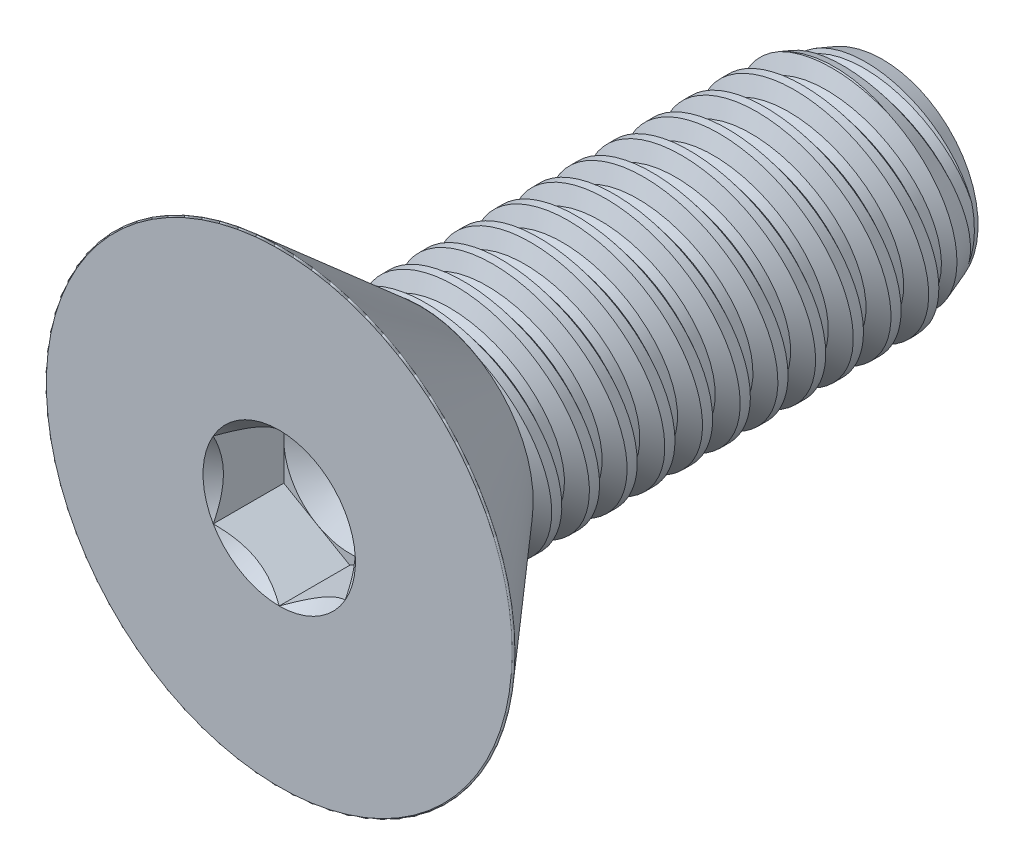
SolidWorks part; units mm, degrees
material "Plain Carbon Steel"
ref_plane "Front" through (0, 0, 0) normal (0, 0, 1) x (1, 0, 0)
ref_plane "Top" through (0, 0, 0) normal (0, 1, 0) x (1, 0, 0)
ref_plane "Right" through (0, 0, 0) normal (1, 0, 0) x (0, 0, -1)
sketch "Sketch1" plane through (0, 0, 0) normal (1, 0, 0) x (0, 0, -1)
  line L0 (0, 0) -> (-5.9436, 0) construction
  line L1 (0, 0) -> (19.4564, 0)
  line L2 (0, 0) -> (0, 4.7625)
  line L3 (0, 4.7625) -> (19.4564, 4.7625)
  line L4 (19.4564, 0) -> (19.4564, 4.7625)
  line L5 (0, -4.7625) -> (19.4564, -4.7625) construction
  dimension "D1" = 19.4564
  dimension "Thread Dia" = 9.525
  dimension "Length" = 25.4
  dimension "Head Height" = 5.9436
revolve "Revolve1" add sketch "Sketch1" angle 360 about L0
ref_plane "Plane1" through (0, 0, 5.9436) normal (0, 0, 1) x (1, 0, 0)
sketch "Sketch2" plane through (0, 0, 0) normal (1, 0, 0) x (0, 0, -1)
  line L0 (0, 4.7625) -> (0, -4.7625) construction
  line L1 (0, -4.7625) -> (1.5875, -4.7625) construction
  line L2 (1.5875, -4.7625) -> (0, 4.7625) construction
  line L3 (0, 4.7625) -> (0.1957, 4.7951) construction
  line L4 (0.1957, 4.7951) -> (1.5659, 5.0235)
  line L5 (1.5659, 5.0235) -> (1.2178, 4.0944)
  line L6 (1.2178, 4.0944) -> (0.8263, 4.0291)
  line L7 (0.8263, 4.0291) -> (0.1957, 4.7951)
  line L8 (1.0221, 4.0617) -> (0.8808, 4.9093) construction
  line L9 (0, -4.7625) -> (19.4564, -4.7625) construction
  line L10 (0, 4.7625) -> (19.4564, 4.7625) construction
  line L12 (0.9053, 4.7625) -> (2.4928, -4.7625) construction
  line L13 (0, -0.2832) -> (3.3981, 0.2832) construction
  line L15 (0, 0) -> (0, 4.7625) construction
  point P19 (1.699, 0)
  dimension "D1" = 60
  dimension "Thread Pitch" = 1.5875
  dimension "D2" = 0.1984
  dimension "D3" = 0.3969
  dimension "D4" = 1.5875
revolve "Cut-Revolve1" cut sketch "Sketch2" angle 360 about L13
sketch "Sketch3" plane through (0, 0, 0) normal (1, 0, 0) x (0, 0, -1)
  line L0 (19.4564, 4.0291) -> (17.4414, 4.7625)
  line L1 (17.4414, 4.7625) -> (19.4564, 4.7625)
  line L2 (19.4564, 4.7625) -> (19.4564, 4.0291)
  line L3 (0, 4.7625) -> (19.4564, 4.7625) construction
  line L4 (19.4564, 0) -> (19.4564, 4.7625) construction
  line L5 (17.4414, 0) -> (0, 0) construction
  line L6 (17.4414, 4.7625) -> (17.4414, -4.7625) construction
  line L7 (0, -4.7625) -> (19.4564, -4.7625) construction
  dimension "D1" = 20
  dimension "D2" = 9.525
revolve "Cut-Revolve2" cut sketch "Sketch3" angle 360 about L5
pattern_linear "LPattern1" count 12 spacing 1.5875 along (0, 0, 1)
pattern_linear "LPattern2" count 2 spacing 1.5875 along (0, 0, 1)
sketch "Sketch4" plane through (0, 0, 0) normal (0, 0, 1) x (1, 0, 0)
  circle A0 centre (0, 0) radius 9.9187
  dimension "Head Dia" = 19.8374
extrude "Extrude1" add sketch "Sketch4" along normal up to surface (5.9436 mm away)
sketch "Sketch9" plane through (0, 0, 0) normal (1, 0, 0) x (0, 0, -1)
  line L0 (-5.9436, 9.9187) -> (0, 4.752)
  line L1 (0, 4.752) -> (0, 9.9187)
  line L2 (0, 9.9187) -> (-5.9436, 9.9187)
  line L3 (0, 0) -> (-5.9436, 0) construction
  line L6 (-5.9436, -9.9187) -> (0, -4.752) construction
  line L7 (0, -9.9187) -> (0, 9.9187) construction
  line L8 (-5.9436, 9.9187) -> (-5.9436, -9.9187) construction
  line L9 (0, 9.9187) -> (-5.9436, 9.9187) construction
  dimension "D1" = 82
revolve "Cut-Revolve3" cut sketch "Sketch9" angle 360 about L3
fillet "Fillet1" radius 0.0508
sketch "Sketch6" plane through (0, 0, 5.9436) normal (0, 0, 1) x (1, 0, 0)
  line L1 (0, -3.2079) -> (2.7781, -1.604)
  line L2 (2.7781, -1.604) -> (2.7781, 1.604)
  line L3 (2.7781, 1.604) -> (0, 3.2079)
  line L4 (0, 3.2079) -> (-2.7781, 1.604)
  line L5 (-2.7781, 1.604) -> (-2.7781, -1.604)
  line L6 (-2.7781, -1.604) -> (0, -3.2079)
  circle A0 centre (0, 0) radius 2.7781 construction
  dimension "Hex" = 5.5562
extrude "Cut-Extrude1" cut sketch "Sketch6" against normal blind 2.9718
sketch "Sketch7" plane through (0, 0, 5.9436) normal (0, 0, 1) x (1, 0, 0)
  circle A0 centre (0, 0) radius 3.2079
extrude "Cut-Extrude4" cut sketch "Sketch7" against normal blind 2.9718 draft 45
sketch "Sketch8" plane through (0, 0, 2.9718) normal (0, 0, 1) x (1, 0, 0)
  circle A0 centre (0, 0) radius 2.7781 construction
  circle A1 centre (0, 0) radius 2.7781
extrude "Cut-Extrude5" cut sketch "Sketch8" against normal blind 0.9906 draft 60
equation "\"D2@Sketch2\"=\"Thread Pitch@Sketch2\"/8"
equation "\"D3@Sketch2\"=\"Thread Pitch@Sketch2\"/4"
equation "\"D4@Sketch2\"=\"Thread Pitch@Sketch2\""
equation "\"D3@LPattern1\"=\"Thread Pitch@Sketch2\""
equation "\"D1@Cut-Extrude1\"=\"Head Height@Sketch1\"/2"
equation "\"D1@Cut-Extrude4\"=\"D1@Cut-Extrude1\""
equation "\"D1@Cut-Extrude5\"=\"D1@Cut-Extrude1\"/3"
equation "\"D1@LPattern1\"=\"D1@Sketch1\"/\"Thread Pitch@Sketch2\""
equation "\"D3@LPattern2\"=\"Thread Pitch@Sketch2\""
